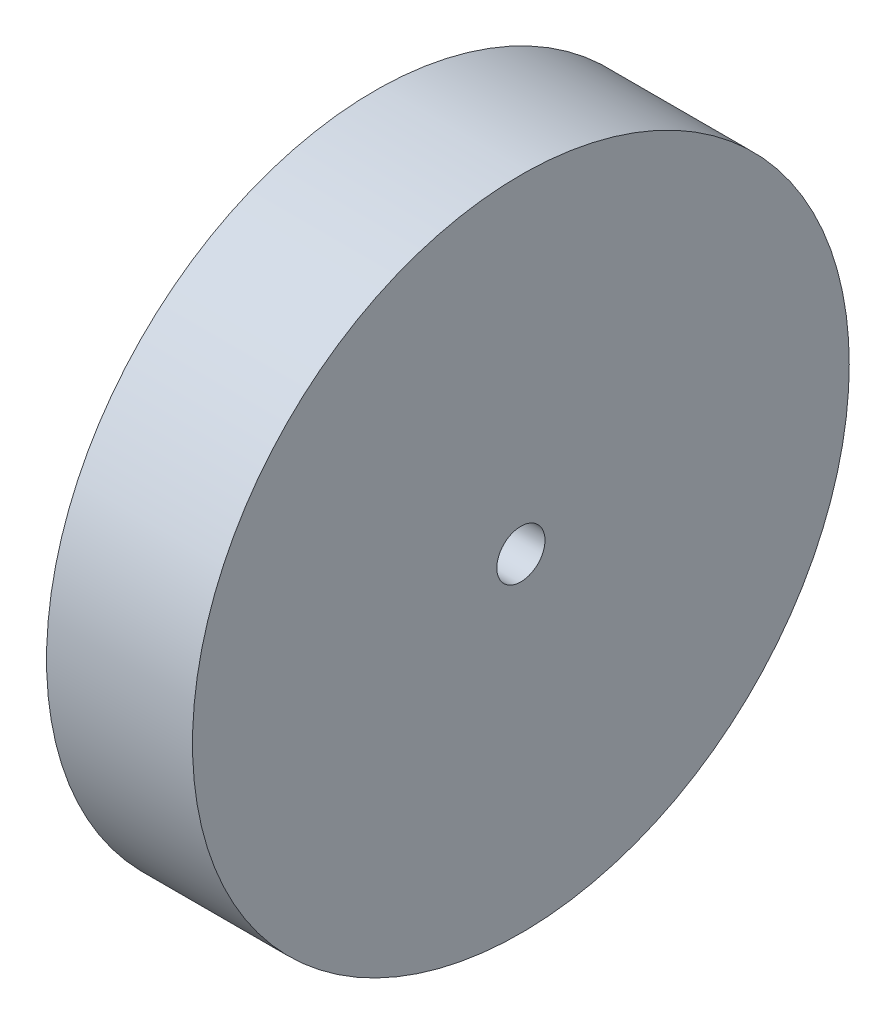
SolidWorks part; units mm, degrees
material "Wheel"
ref_plane "Front Plane" through (0, 0, 0) normal (0, 0, 1) x (1, 0, 0)
ref_plane "Top Plane" through (0, 0, 0) normal (0, 1, 0) x (1, 0, 0)
ref_plane "Right Plane" through (0, 0, 0) normal (1, 0, 0) x (0, 0, -1)
sketch "Sketch1" plane through (0, 0, 0) normal (1, 0, 0) x (0, 0, -1)
  circle A0 centre (0, 0) radius 38.1
  dimension "D1" = 76.2
extrude "Boss-Extrude1" add sketch "Sketch1" along normal blind 16.9333
sketch "Sketch2" plane through (16.9333, 0, 0) normal (1, 0, 0) x (0, 0, -1)
  circle A0 centre (0, 0) radius 2.794
  dimension "D1" = 5.588
extrude "Cut-Extrude1" cut sketch "Sketch2" against normal blind 16.9333
